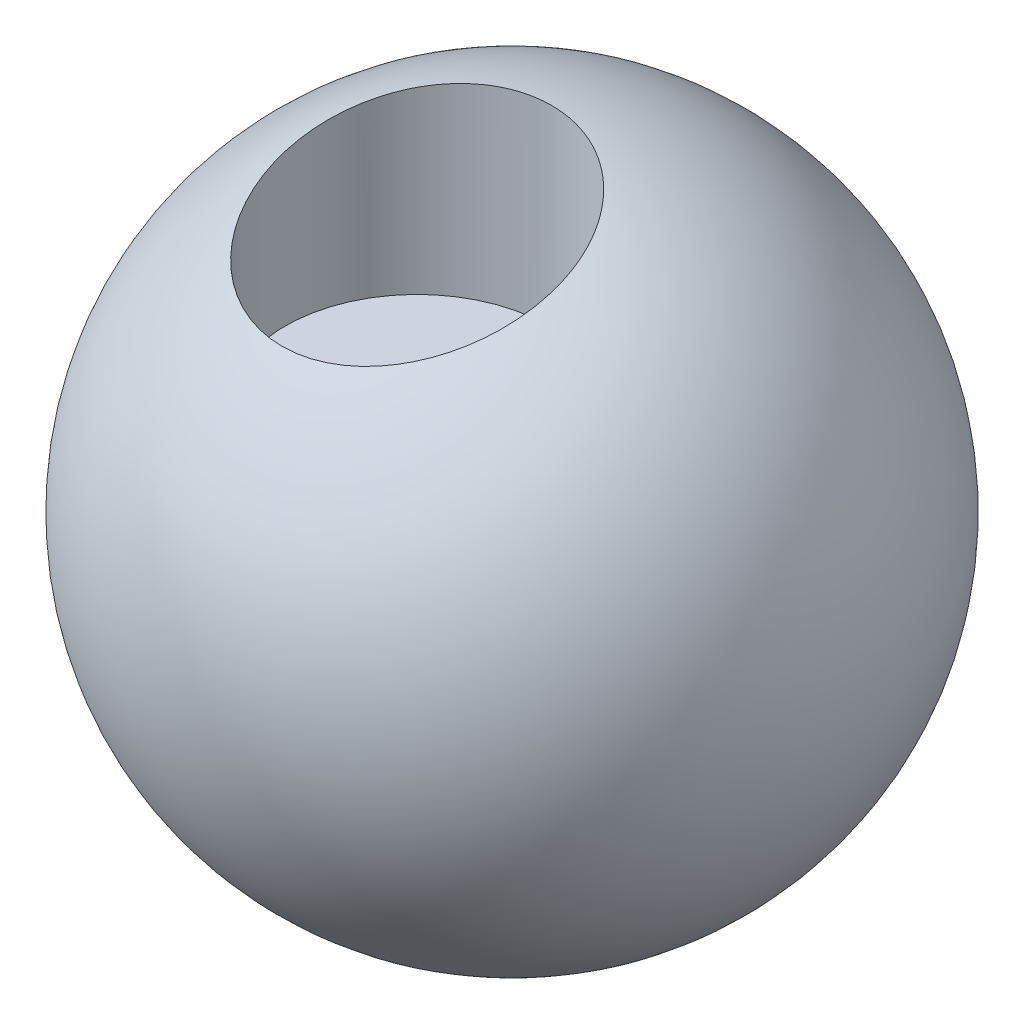
SolidWorks part; units mm, degrees
ref_plane "Front Plane" through (0, 0, 0) normal (0, 0, 1) x (1, 0, 0)
ref_plane "Top Plane" through (0, 0, 0) normal (0, 1, 0) x (1, 0, 0)
ref_plane "Right Plane" through (0, 0, 0) normal (1, 0, 0) x (0, 0, -1)
sketch "Sketch2" plane through (0, 0, 0) normal (0, 0, 1) x (1, 0, 0)
  line L0 (0, 100) -> (0, -100)
  arc A0 (0, 100) -> (0, -100) centre (0, 0) ccw
  dimension "D1" = 200
revolve "Revolve2" add sketch "Sketch2" angle 360 about L0
ref_plane "Plane2" through (0, 100, 0) normal (0, -1, 0) x (-1, 0, 0)
sketch "Sketch6" plane through (-2.538, 100, 26.2322) normal (0, -1, 0) x (-1, 0, 0)
  circle A0 centre (0, 0) radius 40
  dimension "D1" = 80
extrude "Cut-Extrude3" cut sketch "Sketch6" along normal blind 59.2948 contours A0
ref_plane "Plane4" through (0, 100, 0) normal (0, 1, 0) x (1, 0, 0)
ref_plane "Plane6" through (100, 0, 0) normal (1, 0, 0) x (0, 0, -1)
sketch "Sketch13" plane through (0, 0, 0) normal (1, 0, 0) x (0, 0, -1)
  line L0 (0, -72.4423) -> (0, 0) construction
  line L1 (0, 0) -> (75.7393, 0) construction
  circle A0 centre (60, 0) radius 12
  dimension "D1" = 24
  dimension "D2" = 60
  dimension "D3" = 0
extrude "Cut-Extrude7" cut sketch "Sketch13" against normal mid plane 130
ref_plane "Plane8" through (0, 0, -13.7678) normal (0, 0, 1) x (1, 0, 0)
ref_plane "Plane9" through (0, -100, 0) normal (0, -1, 0) x (-1, 0, 0)
